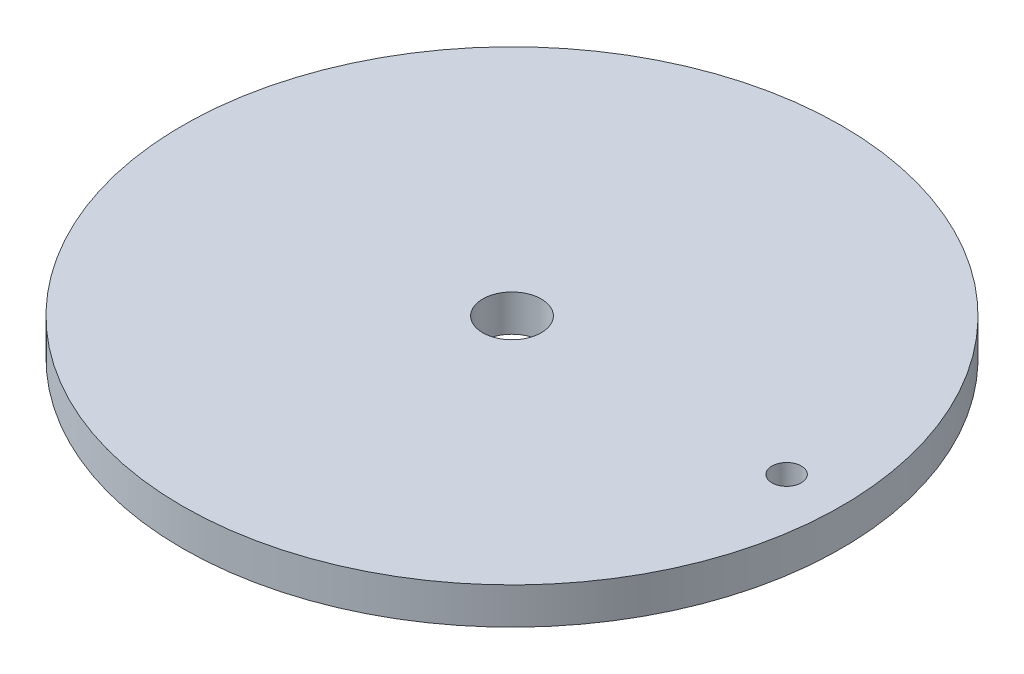
SolidWorks part; units mm, degrees
ref_plane "Front Plane" through (0, 0, 0) normal (0, 0, 1) x (1, 0, 0)
ref_plane "Top Plane" through (0, 0, 0) normal (0, 1, 0) x (1, 0, 0)
ref_plane "Right Plane" through (0, 0, 0) normal (1, 0, 0) x (0, 0, -1)
sketch "Sketch1" plane through (0, 0, 0) normal (0, 1, 0) x (1, 0, 0)
  line L0 (30, 0) -> (45, 0)
  circle A0 centre (0, 0) radius 4
  circle A1 centre (0, 0) radius 30
  circle A2 centre (0, 0) radius 45
  circle A3 centre (37.5, 0) radius 2
  dimension "D1" = 8
  dimension "D2" = 60
  dimension "D3" = 15
  dimension "D4" = 4
extrude "Boss-Extrude1" add sketch "Sketch1" along normal blind 5
